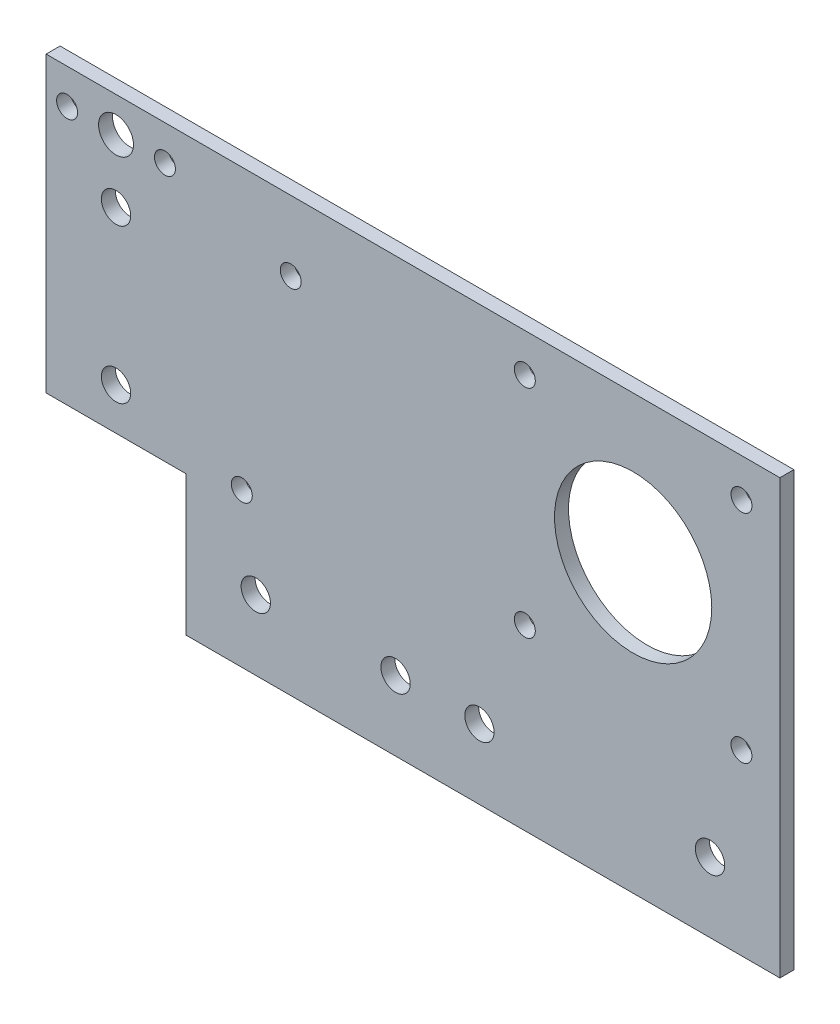
SolidWorks part; units mm, degrees
material "1060 Alloy"
ref_plane "Front Plane" through (0, 0, 0) normal (0, 0, 1) x (1, 0, 0)
ref_plane "Top Plane" through (0, 0, 0) normal (0, 1, 0) x (1, 0, 0)
ref_plane "Right Plane" through (0, 0, 0) normal (1, 0, 0) x (0, 0, -1)
sketch "Sketch1" plane through (0, 0, 0) normal (0, 0, 1) x (1, 0, 0)
  line L0 (0, 0) -> (20, 0)
  line L1 (20, -20) -> (105, -20)
  line L2 (0, 0) -> (0, 42)
  line L3 (0, 42) -> (105, 42)
  line L4 (105, -20) -> (105, 42)
  line L5 (20, 0) -> (20, -20)
  circle A0 centre (3, 37) radius 1.5
  circle A1 centre (17, 37) radius 1.5
  circle A2 centre (84, 21) radius 11.25
  circle A3 centre (99.5, 36.5) radius 1.5
  circle A4 centre (68.5, 36.5) radius 1.5
  circle A5 centre (68.5, 5.5) radius 1.5
  circle A6 centre (99.5, 5.5) radius 1.5
  circle A7 centre (35, 32) radius 1.5
  circle A8 centre (28, 2) radius 1.5
  circle A9 centre (10, 28) radius 2.1
  circle A10 centre (10, 6) radius 2.1
  circle A11 centre (30, -10) radius 2.1
  circle A12 centre (95, -10) radius 2.1
  circle A13 centre (10, 37) radius 2.5
  circle A14 centre (50, -10) radius 2.1
  circle A15 centre (62, -10) radius 2.1
  dimension "D5" = 3
  dimension "D6" = 8
  dimension "D12" = 22.5
  dimension "D18" = 3
  dimension "D19" = 3
  dimension "D20" = 10
  dimension "D22" = 4.2
  dimension "D29" = 10
  dimension "D30" = 5
  dimension "D31" = 20
  dimension "D1" = 20
  dimension "D2" = 20
  dimension "D3" = 42
  dimension "D4" = 85
  dimension "D7" = 15
  dimension "D8" = 5
  dimension "D9" = 3
  dimension "D10" = 14
  dimension "D11" = 21
  dimension "D13" = 31
  dimension "D14" = 31
  dimension "D15" = 15.5
  dimension "D16" = 15.5
  dimension "D17" = 21
  dimension "D21" = 40
  dimension "D23" = 10
  dimension "D24" = 10
  dimension "D25" = 6
  dimension "D26" = 22
  dimension "D27" = 10
  dimension "D28" = 10
  dimension "D32" = 12
extrude "Boss-Extrude1" add sketch "Sketch1" along normal blind 2
